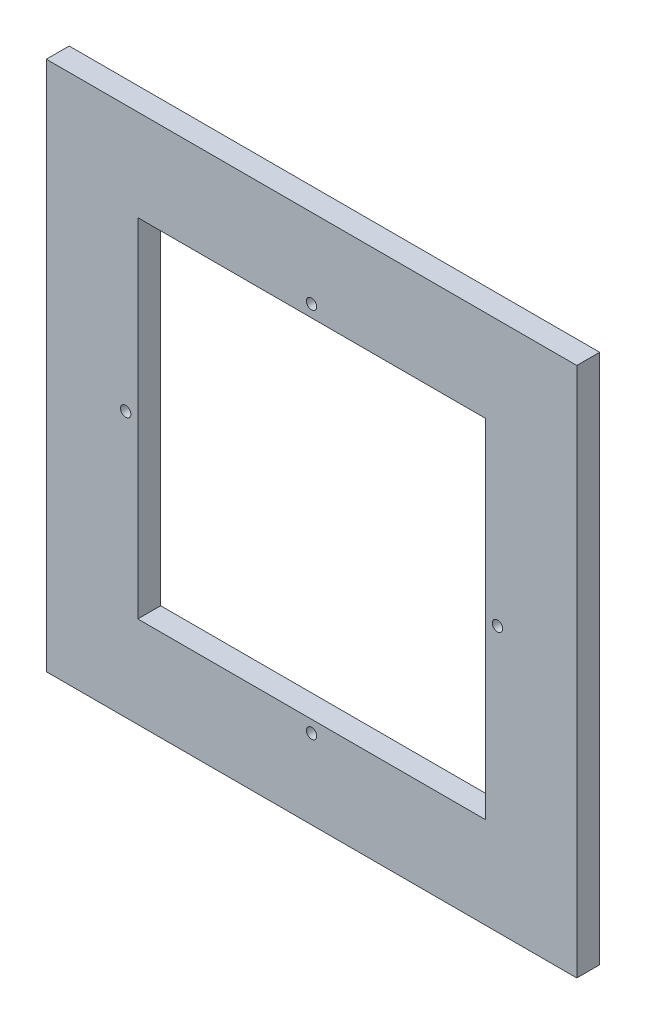
SolidWorks part; units mm, degrees
ref_plane "Front Plane" through (0, 0, 0) normal (0, 0, 1) x (1, 0, 0)
ref_plane "Top Plane" through (0, 0, 0) normal (0, 1, 0) x (1, 0, 0)
ref_plane "Right Plane" through (0, 0, 0) normal (1, 0, 0) x (0, 0, -1)
sketch "Sketch1" plane through (0, 0, 0) normal (0, 0, 1) x (1, 0, 0)
  line L1 (-73.66, 73.66) -> (73.66, 73.66)
  line L2 (-73.66, 73.66) -> (-73.66, 48.26)
  line L3 (-73.66, 48.26) -> (73.66, 48.26)
  line L4 (73.66, 73.66) -> (73.66, 48.26)
  line L5 (73.66, 48.26) -> (48.26, 48.26)
  line L6 (73.66, 48.26) -> (73.66, -48.26)
  line L7 (73.66, -48.26) -> (48.26, -48.26)
  line L8 (48.26, 48.26) -> (48.26, -48.26)
  line L9 (73.66, -48.26) -> (-73.66, -48.26)
  line L10 (73.66, -48.26) -> (73.66, -73.66)
  line L11 (73.66, -73.66) -> (-73.66, -73.66)
  line L12 (-73.66, -48.26) -> (-73.66, -73.66)
  line L13 (-73.66, -48.26) -> (-48.26, -48.26)
  line L14 (-73.66, -48.26) -> (-73.66, 48.26)
  line L15 (-73.66, 48.26) -> (-48.26, 48.26)
  line L16 (-48.26, -48.26) -> (-48.26, 48.26)
  circle A0 centre (0, 0) radius 51.6255 construction
  circle A1 centre (0, 0) radius 45.72 construction
  circle A2 centre (0, 51.6255) radius 1.4351
  circle A3 centre (51.6255, 0) radius 1.4351
  circle A4 centre (0, -51.6255) radius 1.4351
  circle A5 centre (-51.6255, 0) radius 1.4351
  point P27 (0, 0)
  dimension "D1" = 25.4
  dimension "D5" = 91.44
  dimension "D6" = 103.251
  dimension "D11" = 2.8702
  dimension "D2" = 25.4
  dimension "D3" = 25.4
  dimension "D4" = 25.4
  dimension "D7" = 48.26
  dimension "D8" = 48.26
  dimension "D9" = 48.26
  dimension "D10" = 48.26
  dimension "D12" = 4
extrude "Boss-Extrude1" add sketch "Sketch1" along normal blind 6.35 contours L4 L1 L2 L3 A2 | L9 L16 L3 L14 A5 | L3 L8 L7 L6 A3 | L9 L12 L11 L10 L7 A4
